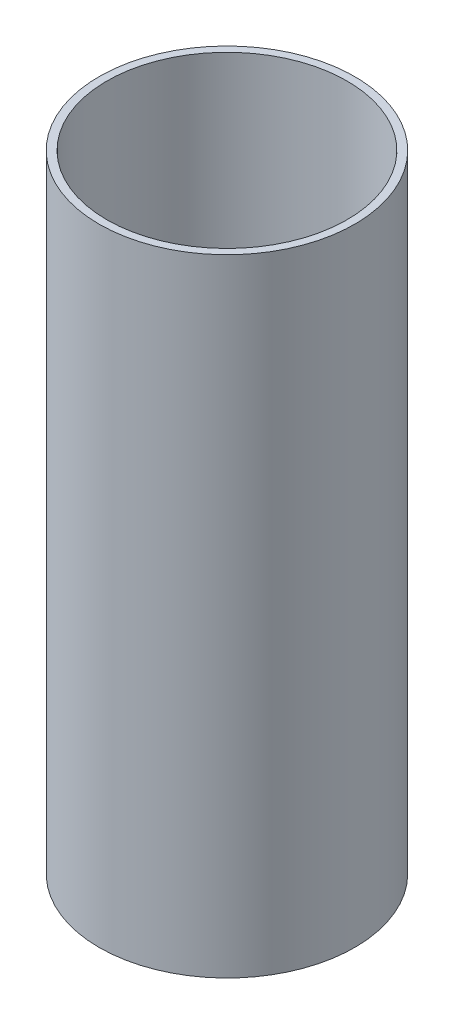
SolidWorks part; units mm, degrees
material "6063-T6"
ref_plane "Front Plane" through (0, 0, 0) normal (0, 0, 1) x (1, 0, 0)
ref_plane "Top Plane" through (0, 0, 0) normal (0, 1, 0) x (1, 0, 0)
ref_plane "Right Plane" through (0, 0, 0) normal (1, 0, 0) x (0, 0, -1)
sketch "Sketch1" plane through (0, 0, 0) normal (0, 1, 0) x (1, 0, 0)
  circle A0 centre (0, 0) radius 50
  circle A1 centre (0, 0) radius 47
  dimension "D1" = 100
  dimension "D2" = 3
extrude "Boss-Extrude1" add sketch "Sketch1" along normal blind 245
